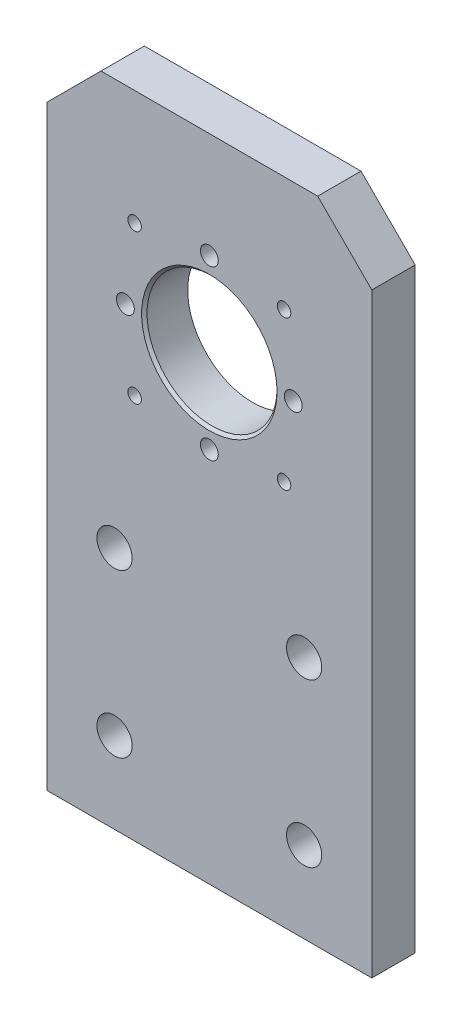
SolidWorks part; units mm, degrees
ref_plane "Front Plane" through (0, 0, 0) normal (0, 0, 1) x (1, 0, 0)
ref_plane "Top Plane" through (0, 0, 0) normal (0, 1, 0) x (1, 0, 0)
ref_plane "Right Plane" through (0, 0, 0) normal (1, 0, 0) x (0, 0, -1)
sketch "Sketch1" plane through (0, 0, 0) normal (0, 0, 1) x (1, 0, 0)
  line L1 (30, -60) -> (-30, -60)
  line L2 (30, -60) -> (30, 60)
  line L3 (30, 60) -> (-30, 60)
  line L4 (-30, -60) -> (-30, 60)
  line L5 (30, -60) -> (-30, 60) construction
  line L6 (30, 60) -> (-30, -60) construction
  circle A0 centre (-17.5, -15) radius 3.25
  circle A1 centre (-17.5, -45) radius 3.25
  circle A2 centre (17.5, -45) radius 3.25
  circle A3 centre (17.5, -15) radius 3.25
  circle A4 centre (0, 25) radius 12
  point P0 (0, 0)
  dimension "D3" = 6.5
  dimension "D7" = 24
  dimension "D1" = 60
  dimension "D2" = 120
  dimension "D4" = 12.5
  dimension "D5" = 30
  dimension "D6" = 15
  dimension "D8" = 85
extrude "Boss-Extrude1" add sketch "Sketch1" along normal blind 8
sketch "Sketch2" plane through (0, 0, 8) normal (0, 0, 1) x (1, 0, 0)
  line L0 (0, 25) -> (-40.1431, 65.1431)
  line L1 (0, 25) -> (0, 60)
  line L2 (30, 60) -> (-30, 60) construction
  line L3 (30, 25) -> (-30, 25)
  line L4 (-30, 60) -> (-30, -60) construction
  line L5 (0, 25) -> (-40.1431, -15.1431)
  line L6 (0, 25) -> (40.1431, -15.1431)
  line L7 (0, 25) -> (40.1431, 65.1431)
  circle A0 centre (0, 25) radius 19.5
  circle A1 centre (0, 25) radius 15.5
  dimension "D1" = 31
  dimension "D2" = 39
  dimension "D3" = 45
hole_wizard "M3 Tapped Hole1" positions "Sketch3" profile "Sketch4" tap size "M3" standard "ISO" end condition through all
sketch "Sketch3" plane through (0, 0, 8) normal (0, 0, 1) x (1, 0, 0)
  line L0 (0, 25) -> (-40.1431, 65.1431) construction
  line L1 (0, 25) -> (-40.1431, -15.1431) construction
  line L2 (0, 25) -> (40.1431, -15.1431) construction
  line L3 (0, 25) -> (40.1431, 65.1431) construction
  circle A0 centre (0, 25) radius 19.5 construction
  point P0 (-13.7886, 38.7886)
  point P6 (-13.7886, 11.2114)
  point P10 (13.7886, 11.2114)
  point P14 (13.7886, 38.7886)
sketch "Sketch4" plane through (-13.7886, 38.7886, 8) normal (1, 0, 0) x (0, -1, 0)
  line L0 (0, 0) -> (0, 8)
  line L1 (0, 8) -> (1.25, 8)
  line L2 (1.25, 8) -> (1.25, 0)
  line L5 (1.25, 0) -> (0, 0)
  line L11 (0, -6.35) -> (0, 107.95) construction
  dimension "Thru Tap Drill Dia." = 2.5
  dimension "Thru Tap Drill Depth" = 8
cosmetic thread "Hole Thread1" parameters "D2"=3
cosmetic thread "Hole Thread2" parameters "D2"=3
cosmetic thread "Hole Thread3" parameters "D2"=3
cosmetic thread "Hole Thread4" parameters "D2"=3
hole_wizard "M4 Tapped Hole1" positions "Sketch9" profile "Sketch10" tap size "M4" standard "ISO" end condition through all
sketch "Sketch9" plane through (0, 0, 8) normal (0, 0, 1) x (1, 0, 0)
  line L0 (30, 25) -> (-30, 25) construction
  line L1 (0, 25) -> (0, 60) construction
  circle A0 centre (0, 25) radius 15.5 construction
  point P0 (-15.5, 25)
  point P6 (0, 40.5)
  point P10 (15.5, 25)
  point P12 (0, 9.5)
sketch "Sketch10" plane through (-15.5, 25, 8) normal (1, 0, 0) x (0, -1, 0)
  line L0 (0, 0) -> (0, 8)
  line L1 (0, 8) -> (1.65, 8)
  line L2 (1.65, 8) -> (1.65, 0)
  line L5 (1.65, 0) -> (0, 0)
  line L11 (0, -6.35) -> (0, 107.95) construction
  dimension "Thru Tap Drill Dia." = 3.3
  dimension "Thru Tap Drill Depth" = 8
cosmetic thread "Hole Thread5" parameters "D2"=4
cosmetic thread "Hole Thread6" parameters "D2"=4
cosmetic thread "Hole Thread7" parameters "D2"=4
cosmetic thread "Hole Thread8" parameters "D2"=4
chamfer "Chamfer1" distance 0.5 angle 45 1 edges at (12, 25, 8)
chamfer "Chamfer2" distance 10 angle 45 2 edges at (30, 60, 4) (-30, 60, 4)
